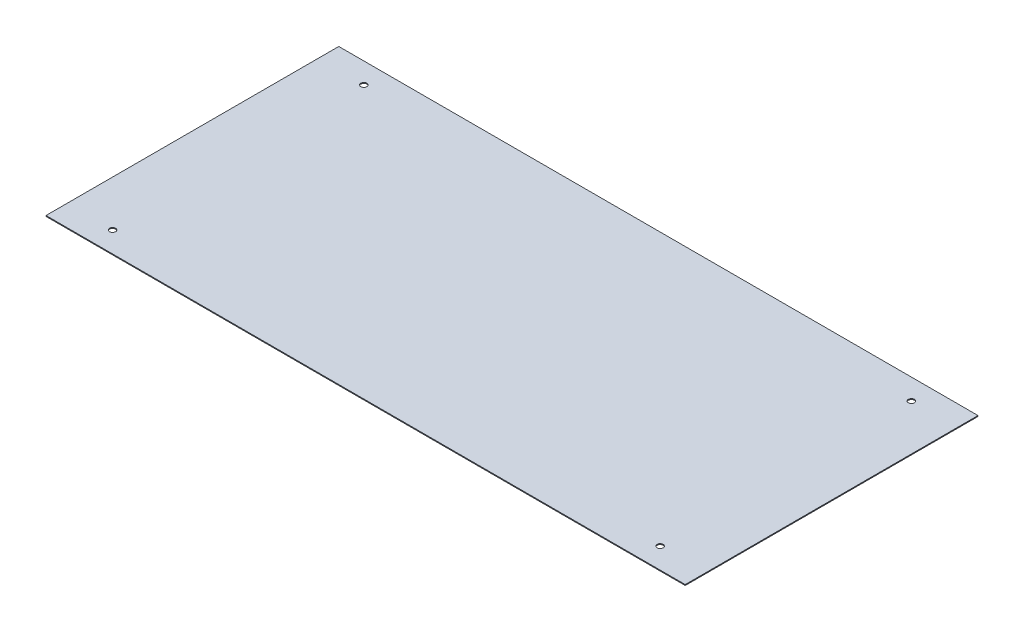
SolidWorks part; units mm, degrees
material "AISI 304"
ref_plane "Front Plane" through (0, 0, 0) normal (0, 0, 1) x (1, 0, 0)
ref_plane "Top Plane" through (0, 0, 0) normal (0, 1, 0) x (1, 0, 0)
ref_plane "Right Plane" through (0, 0, 0) normal (1, 0, 0) x (0, 0, -1)
sketch "Sketch2" plane through (0, 0, 0) normal (0, 1, 0) x (1, 0, 0)
  line L1 (369, -169) -> (-369, -169)
  line L2 (369, -169) -> (369, 169)
  line L3 (369, 169) -> (-369, 169)
  line L4 (-369, -169) -> (-369, 169)
  circle A1 centre (-316.0619, 145) radius 3.5
  circle A3 centre (-316.0619, -145) radius 3.5
  circle A5 centre (316.0619, -145) radius 3.5
  circle A7 centre (316.0619, 145) radius 3.5
  point P0 (0, 0)
  point P7 (-369, 0)
  point P8 (0, -169)
  dimension "D7" = 7
  dimension "D1" = 738
  dimension "D2" = 338
  dimension "D3" = 24
  dimension "D4" = 24
  dimension "D5" = 52.9381
  dimension "D6" = 52.9381
extrude "Boss-Extrude1" add sketch "Sketch2" along normal blind 1
